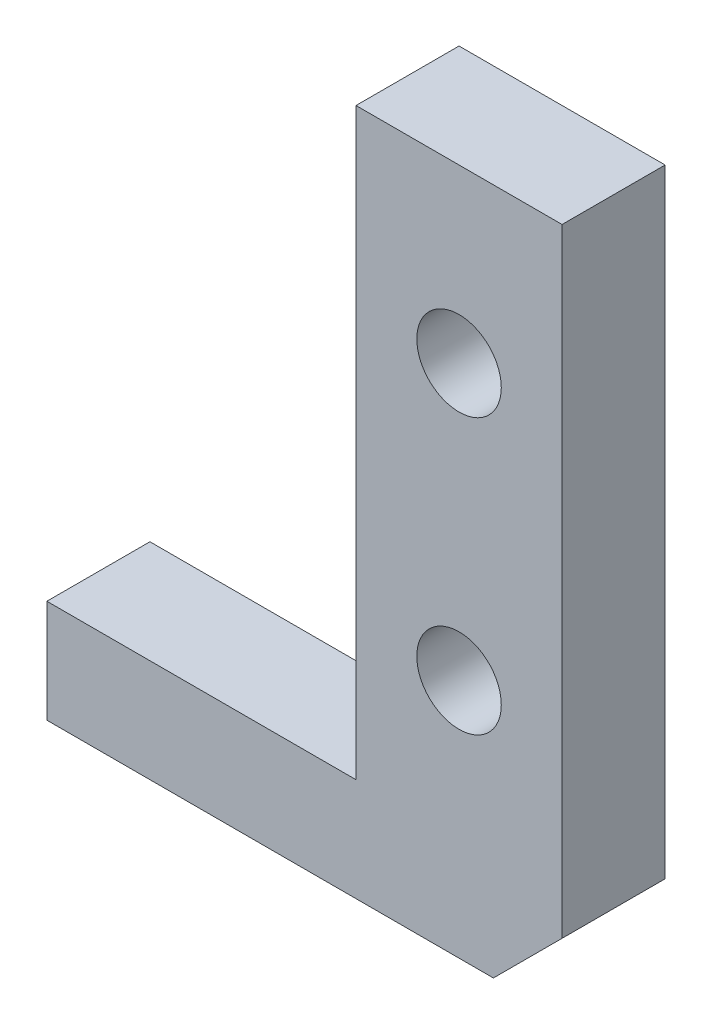
SolidWorks part; units mm, degrees
ref_plane "Front Plane" through (0, 0, 0) normal (0, 0, 1) x (1, 0, 0)
ref_plane "Top Plane" through (0, 0, 0) normal (0, 1, 0) x (1, 0, 0)
ref_plane "Right Plane" through (0, 0, 0) normal (1, 0, 0) x (0, 0, -1)
sketch "Sketch1" plane through (0, 0, 0) normal (0, 0, 1) x (1, 0, 0)
  line L0 (0, 0) -> (13, 0)
  line L1 (13, 0) -> (15, 2)
  line L2 (15, 2) -> (15, 20)
  line L3 (15, 20) -> (9, 20)
  line L4 (9, 20) -> (9, 3)
  line L5 (9, 3) -> (0, 3)
  line L6 (0, 3) -> (0, 0)
  point P8 (15, 3.6633)
  dimension "D1" = 15
  dimension "D2" = 20
  dimension "D3" = 9
  dimension "D4" = 3
  dimension "D5" = 135
  dimension "D6" = 2
extrude "Boss-Extrude1" add sketch "Sketch1" along normal blind 3
sketch "Sketch2" plane through (0, 0, 3) normal (0, 0, 1) x (1, 0, 0)
  line L0 (15, 20) -> (9, 20) construction
  circle A0 centre (12, 15) radius 1.23
  circle A1 centre (12, 7) radius 1.23
  point P4 (0, 0)
  point P7 (12, 20)
  dimension "D2" = 5
  dimension "D3" = 2.46
  dimension "D1" = 8
extrude "Cut-Extrude1" cut sketch "Sketch2" against normal through all
